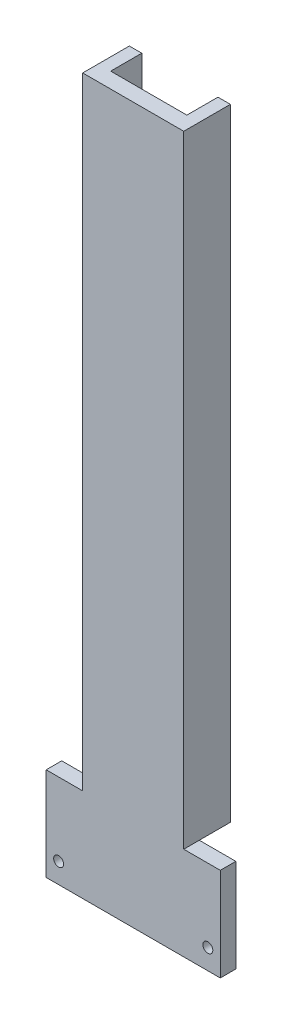
SolidWorks part; units mm, degrees
ref_plane "前视基准面" through (0, 0, 0) normal (0, 0, 1) x (1, 0, 0)
ref_plane "上视基准面" through (0, 0, 0) normal (0, 1, 0) x (1, 0, 0)
ref_plane "右视基准面" through (0, 0, 0) normal (1, 0, 0) x (0, 0, -1)
sketch "Sketch1" plane through (0, 0, 0) normal (0, 1, 0) x (1, 0, 0)
  line L0 (0, 0) -> (0, -15)
  line L1 (0, -15) -> (32.5, -15)
  line L2 (32.5, -15) -> (32.5, 0)
  line L3 (32.5, 0) -> (28.5, 0)
  line L4 (28.5, 0) -> (28.5, -10)
  line L5 (28.5, -10) -> (4, -10)
  line L6 (4, -10) -> (4, 0)
  line L7 (4, 0) -> (0, 0)
  dimension "D1" = 4
  dimension "D2" = 4
  dimension "D3" = 24.5
  dimension "D4" = 5
  dimension "D5" = 10
extrude "Boss-Extrude1" add sketch "Sketch1" along normal blind 200
sketch "Sketch2" plane through (0, 0, 15) normal (0, 0, 1) x (1, 0, 0)
  line L0 (32.5, 0) -> (44.25, 0)
  line L1 (44.25, 0) -> (44.25, -30)
  line L2 (44.25, -30) -> (-11.75, -30)
  line L3 (-11.75, -30) -> (-11.75, 0)
  line L4 (-11.75, 0) -> (0, 0)
  line L5 (32.5, 0) -> (0, 0)
  dimension "D1" = 56
  dimension "D2" = 11.75
  dimension "D3" = 30
extrude "Boss-Extrude2" add sketch "Sketch2" against normal blind 5 contours L2 L3 L4 L5 L0 L1
hole_wizard "M3 Clearance Hole1" positions "Sketch4" profile "Sketch5" hole size "M3" standard "GB" end condition through all
sketch "Sketch4" plane through (0, 0, 10) normal (0, 0, -1) x (-1, 0, 0)
  line L0 (-44.25, 0) -> (-44.25, -30) construction
  line L3 (11.75, 0) -> (0, 0) construction
  point P0 (7.75, -23.5)
  point P2 (-40.25, -23.5)
  point P9 (-44.25, -19.5899)
  point P14 (0, 0)
  point P15 (7.75, -18.8342)
  dimension "D1" = 48
  dimension "D2" = 4
  dimension "D3" = 23.5
sketch "Sketch5" plane through (-7.75, -23.5, 10) normal (1, 0, 0) x (0, 1, 0)
  line L0 (0, 0) -> (0, 5)
  line L1 (0, 5) -> (1.6, 5)
  line L2 (1.6, 5) -> (1.6, 0.025)
  line L3 (1.6, 0.025) -> (1.625, 0)
  line L5 (1.625, 0) -> (0, 0)
  line L6 (-1.6, 0.025) -> (-1.625, 0) construction
  line L11 (0, -6.35) -> (0, 107.95) construction
  dimension "Thru Hole Dia." = 3.2
  dimension "Thru Hole Depth" = 5
  dimension "Near C'Sink Dia." = 3.25
  dimension "Near C'Sink Angle" = 90
